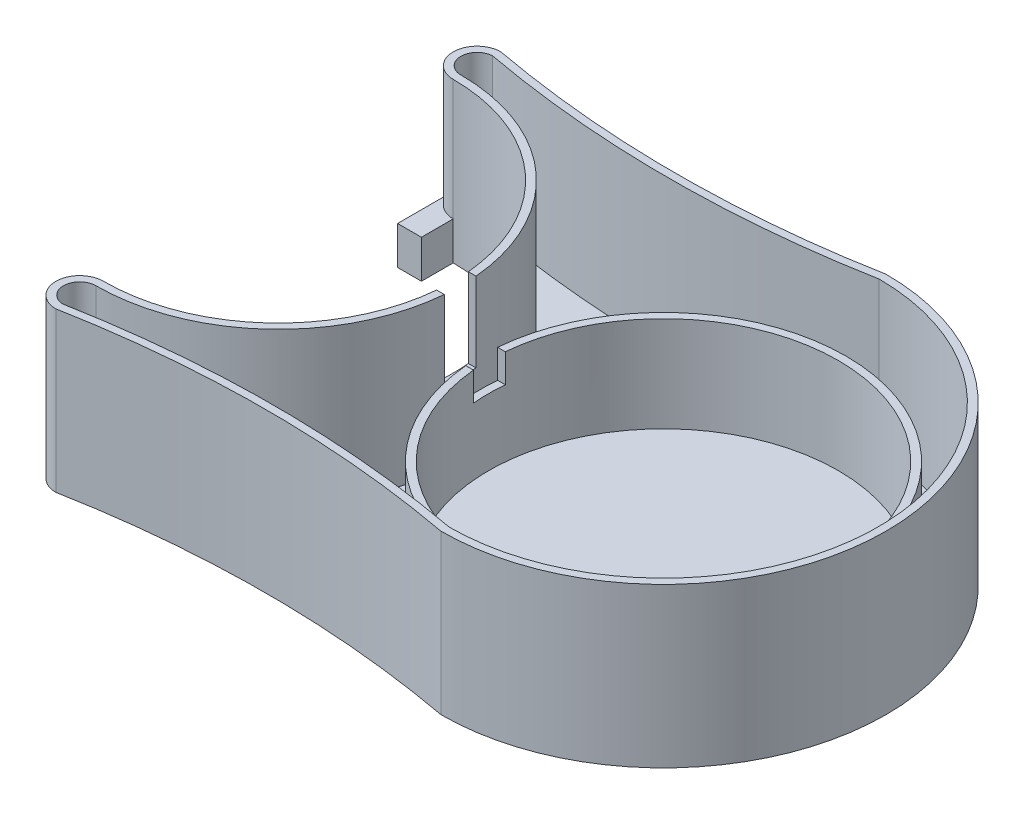
SolidWorks part; units mm, degrees
ref_plane "Alzado" through (0, 0, 0) normal (0, 0, 1) x (1, 0, 0)
ref_plane "Planta" through (0, 0, 0) normal (0, 1, 0) x (1, 0, 0)
ref_plane "Vista lateral" through (0, 0, 0) normal (1, 0, 0) x (0, 0, -1)
sketch "Croquis1" plane through (0, 0, 0) normal (0, 1, 0) x (1, 0, 0)
  line L0 (0, 35) -> (0, -35) construction
  line L1 (-65, -35) -> (65, -35) construction
  line L2 (-65, -35) -> (-65, 35) construction
  line L3 (-65, 35) -> (65, 35) construction
  line L4 (65, -35) -> (65, 35) construction
  line L5 (-65, -35) -> (65, 35) construction
  line L6 (-65, 35) -> (65, -35) construction
  line L7 (0, 0) -> (65, 0) construction
  line L8 (0, 0) -> (-65, 0) construction
  circle A0 centre (37.5, 0) radius 27.5
  arc A1 (-23.0713, -27.5) -> (-23.0713, 27.5) centre (-23.0713, 0) ccw
  arc A2 (-23.0713, 35) -> (-23.0713, 27.5) centre (-23.0713, 31.25) ccw
  arc A3 (-23.0713, -27.5) -> (-23.0713, -35) centre (-23.0713, -31.25) ccw
  arc A4 (-23.0713, 35) -> (37.5, 35) centre (7.2144, 197.1967) ccw
  arc A5 (-23.0713, -35) -> (37.5, -35) centre (7.2144, -197.1967) cw
  arc A6 (37.5, 35) -> (37.5, -35) centre (37.5, 0) cw
  point P0 (0, 0)
  point P14 (37.5, 35)
  point P15 (-23.0713, 27.5)
  point P16 (-23.0713, -27.5)
  point P17 (-23.0713, 35)
  point P18 (-23.0713, -35)
  point P25 (37.5, -35)
  dimension "D3" = 55
  dimension "D4" = 165
  dimension "D1" = 130
  dimension "D2" = 70
extrude "Saliente-Extruir1" add sketch "Croquis1" along normal blind 25
shell "Vaciado3" thickness 1.2
sketch "Croquis5" plane through (0, 25, 0) normal (0, 1, 0) x (1, 0, 0)
  circle A0 centre (37.5, 0) radius 29.5
extrude "Cortar-Extruir1" cut sketch "Croquis5" against normal blind 8
sketch "Croquis6" plane through (0, 0, 0) normal (0, -1, 0) x (1, 0, 0)
  circle A0 centre (37.5, 0) radius 27.5
extrude "Saliente-Extruir4" add sketch "Croquis6" against normal blind 2
sketch "Croquis7" plane through (0, 25, 0) normal (0, 1, 0) x (1, 0, 0)
  line L0 (-26.8213, 31.25) -> (-26.8213, -31.25) construction
  line L1 (-26.8213, 31.25) -> (-26.8213, 27.5)
  line L2 (-24.9463, 27.5) -> (-24.9463, 22.5) construction
  line L3 (-26.8213, 0) -> (4.4287, 0) construction
  line L4 (-26.8213, 27.5) -> (-23.0713, 27.5)
  line L5 (-26.8213, 27.5) -> (-26.8213, 22.5)
  line L6 (-26.8213, 22.5) -> (-23.0713, 22.5)
  line L7 (-23.0713, 27.5) -> (-23.0713, 22.5)
  line L8 (-26.8213, 27.5) -> (-23.0713, 22.5) construction
  line L9 (-26.8213, 22.5) -> (-23.0713, 27.5) construction
  line L10 (-23.0713, -27.5) -> (-23.0713, -22.5)
  line L11 (-26.8213, -22.5) -> (-23.0713, -22.5)
  line L12 (-26.8213, -27.5) -> (-26.8213, -22.5)
  line L13 (-26.8213, -27.5) -> (-26.8213, -31.25)
  line L14 (-26.8213, -31.25) -> (-26.7899, -31.2782)
  arc A0 (-23.0713, 35) -> (-23.0713, 27.5) centre (-23.0713, 31.25) ccw construction
  arc A1 (-23.0713, -27.5) -> (-23.0713, -35) centre (-23.0713, -31.25) ccw construction
  arc A2 (-26.8213, 31.25) -> (-23.0713, 27.5) centre (-23.0713, 31.25) ccw
  arc A3 (-23.0713, -27.5) -> (-23.0713, 27.5) centre (-23.0713, 0) ccw construction
  arc A4 (-26.8213, -31.25) -> (-23.0713, -27.5) centre (-23.0713, -31.25) cw
  arc A5 (-23.0713, -27.5) -> (-26.8213, -31.25) centre (-23.0713, -31.25) ccw
  point P13 (-24.9463, 25)
  point P27 (-24.9463, -25)
  arc M8 (-23.0713, 35) -> (-23.0713, 27.5) centre (-23.0713, 31.25) ccw
  arc M10 (-23.0713, -27.5) -> (-23.0713, -35) centre (-23.0713, -31.25) ccw
  dimension "D1" = 5
extrude "Saliente-Extruir5" add sketch "Croquis7" against normal blind 25 separate body contours L12 L13 L10 L11 M10 | L1 L4 M8 | L7 L4 L5 L6
sketch "Croquis8" plane through (0, 25, 0) normal (0, 1, 0) x (1, 0, 0)
  line L0 (-26.8213, 31.25) -> (-26.8213, 22.5) construction
  line L1 (-23.0713, 27.5) -> (-23.0713, 22.5) construction
  line L2 (-26.8213, 22.5) -> (-23.0713, 22.5) construction
  line L3 (-26.8213, -22.5) -> (-23.0713, -22.5) construction
  line L4 (-26.8213, -31.25) -> (-26.8213, -22.5) construction
  line L5 (-23.0713, -27.5) -> (-23.0713, -22.5) construction
  line L6 (-26.8213, 31.25) -> (-26.8213, 22.5)
  line L7 (-23.0713, 27.5) -> (-23.0713, 22.5)
  line L8 (-26.8213, 22.5) -> (-23.0713, 22.5)
  line L9 (-26.8213, -22.5) -> (-23.0713, -22.5)
  line L10 (-26.8213, -31.25) -> (-26.8213, -22.5)
  line L11 (-23.0713, -27.5) -> (-23.0713, -22.5)
  arc A0 (-26.8213, 31.25) -> (-23.0713, 27.5) centre (-23.0713, 31.25) ccw
  arc A1 (-23.0713, -27.5) -> (-26.8213, -31.25) centre (-23.0713, -31.25) ccw
  arc A2 (-23.0713, -27.5) -> (-26.8213, -31.25) centre (-23.0713, -31.25) ccw
  arc M14 (-23.0713, 35) -> (-23.0713, 27.5) centre (-23.0713, 31.25) ccw
  arc M16 (-23.0713, -27.5) -> (-23.0713, -35) centre (-23.0713, -31.25) ccw
extrude "Cortar-Extruir2" cut sketch "Croquis8" against normal blind 19 contours L6 L8 L7 M14 | L11 L9 L10 M16
sketch "Croquis9" plane through (0, 25, 0) normal (0, 1, 0) x (1, 0, 0)
  line L0 (0, 0) -> (72.5, 0) construction
  line L2 (0.4356, 2.5) -> (15.4289, 2.5)
  line L3 (0.4356, 2.5) -> (0.4356, -2.5)
  line L4 (0.4356, -2.5) -> (15.4289, -2.5)
  line L5 (15.4289, 2.5) -> (15.4289, -2.5)
  line L6 (0.4356, 2.5) -> (15.4289, -2.5) construction
  line L7 (0.4356, -2.5) -> (15.4289, 2.5) construction
  arc A0 (37.5, -35) -> (37.5, 35) centre (37.5, 0) ccw construction
  point P6 (7.9322, 0)
  dimension "D1" = 5
extrude "Cortar-Extruir3" cut sketch "Croquis9" against normal blind 12.5
